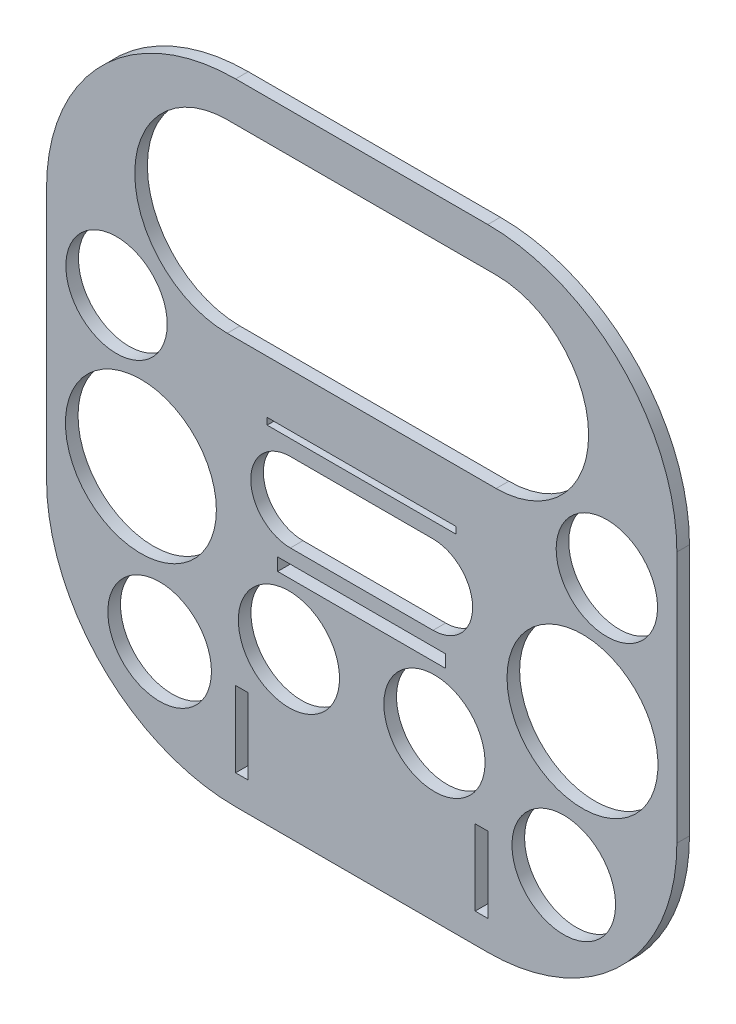
SolidWorks part; units mm, degrees
ref_plane "Front Plane" through (0, 0, 0) normal (0, 0, 1) x (1, 0, 0)
ref_plane "Top Plane" through (0, 0, 0) normal (0, 1, 0) x (1, 0, 0)
ref_plane "Right Plane" through (0, 0, 0) normal (1, 0, 0) x (0, 0, -1)
sketch "Sketch1" plane through (0, 0, 0) normal (0, 0, 1) x (1, 0, 0)
  line L0 (0, 53.5) -> (0, -96.5) construction
  line L1 (-75, 53.5) -> (75, 53.5) construction
  line L2 (-75, 53.5) -> (-75, -96.5) construction
  line L3 (-75, -96.5) -> (75, -96.5) construction
  line L4 (75, 53.5) -> (75, -96.5) construction
  line L5 (-30, 53.5) -> (30, 53.5)
  line L6 (-30, -96.5) -> (30, -96.5) construction
  line L7 (-75, 8.5) -> (75, 8.5) construction
  line L8 (-75, 8.5) -> (-75, -51.5)
  line L9 (-75, -51.5) -> (75, -51.5) construction
  line L10 (75, 8.5) -> (75, -51.5)
  line L11 (-30, -96.5) -> (-0.5, -96.5)
  line L12 (0.5, -96.5) -> (30, -96.5)
  line L13 (-0.5, -96.5) -> (0.5, -96.5)
  arc A0 (-75, 8.5) -> (-30, 53.5) centre (-30, 8.5) cw
  arc A1 (30, 53.5) -> (75, 8.5) centre (30, 8.5) cw
  arc A2 (-75, -51.5) -> (-30, -96.5) centre (-30, -51.5) ccw
  arc A3 (30, -96.5) -> (75, -51.5) centre (30, -51.5) ccw
  point P10 (0, 53.5)
  point P19 (0, -96.5)
  dimension "D3" = 45
  dimension "D4" = 45
  dimension "D1" = 150
  dimension "D2" = 150
  dimension "D5" = 53.5
extrude "Boss-Extrude1" add sketch "Sketch1" along normal blind 3
sketch "Sketch2" plane through (0, 0, 3) normal (0, 0, 1) x (1, 0, 0)
  line L0 (0, -1.65) -> (0, 1.65) construction
  line L1 (-30, -71.5) -> (-27, -71.5)
  line L2 (-30, -71.5) -> (-30, -89.5)
  line L3 (-30, -89.5) -> (-27, -89.5)
  line L4 (-27, -71.5) -> (-27, -89.5)
  line L5 (30, -89.5) -> (27, -89.5)
  line L6 (27, -71.5) -> (27, -89.5)
  line L7 (30, -71.5) -> (27, -71.5)
  line L8 (30, -71.5) -> (30, -89.5)
  line L9 (-30, -96.5) -> (30, -96.5) construction
  line L10 (-32, 22.0933) -> (32, 22.0933) construction
  line L11 (-22.5, -12.5) -> (22.5, -12.5)
  line L12 (-22.5, -12.5) -> (-22.5, -14.1)
  line L13 (-22.5, -14.1) -> (22.5, -14.1)
  line L14 (22.5, -12.5) -> (22.5, -14.1)
  line L15 (-20, -43) -> (20, -43)
  line L16 (-20, -43) -> (-20, -40)
  line L17 (-20, -40) -> (20, -40)
  line L18 (20, -43) -> (20, -40)
  line L19 (-20, -43) -> (20, -40) construction
  line L20 (-20, -40) -> (20, -43) construction
  line L21 (-32, 44.0933) -> (32, 44.0933)
  line L22 (-32, 0.0933) -> (32, 0.0933)
  line L23 (-16.9725, -27.2223) -> (16.9725, -27.2223) construction
  line L24 (-16.9725, -17.7994) -> (16.9725, -17.7994)
  line L25 (-16.9725, -36.6452) -> (16.9725, -36.6452)
  circle A1 centre (-17.3155, -57.6917) radius 12.0391
  circle A2 centre (-48.0822, -71.5) radius 12.3239
  arc A3 (-32, 44.0933) -> (-32, 0.0933) centre (-32, 22.0933) ccw
  arc A4 (32, 0.0933) -> (32, 44.0933) centre (32, 22.0933) ccw
  circle A5 centre (48.0822, -71.5) radius 12.3239
  circle A6 centre (17.3155, -57.6917) radius 12.0391
  arc A8 (-16.9725, -17.7994) -> (-16.9725, -36.6452) centre (-16.9725, -27.2223) ccw
  arc A9 (16.9725, -36.6452) -> (16.9725, -17.7994) centre (16.9725, -27.2223) ccw
  circle A10 centre (-58.3377, -5.2171) radius 12.0625
  circle A11 centre (-52.5411, -37.6265) radius 17.9592
  circle A13 centre (52.5411, -37.6265) radius 17.9592
  circle A15 centre (58.3377, -5.2171) radius 12.0625
  point P16 (0, -12.5)
  point P17 (0, -41.5)
  point P30 (0, 22.0933)
  point P43 (0, -27.2223)
  dimension "D12" = 22
  dimension "D1" = 3
  dimension "D2" = 18
  dimension "D3" = 7
  dimension "D4" = 54
  dimension "D5" = 45
  dimension "D6" = 1.6
  dimension "D7" = 82.4
  dimension "D8" = 40
  dimension "D9" = 3
  dimension "D10" = 53.5
  dimension "D13" = 64
extrude "Cut-Extrude1" cut sketch "Sketch2" against normal blind 10
